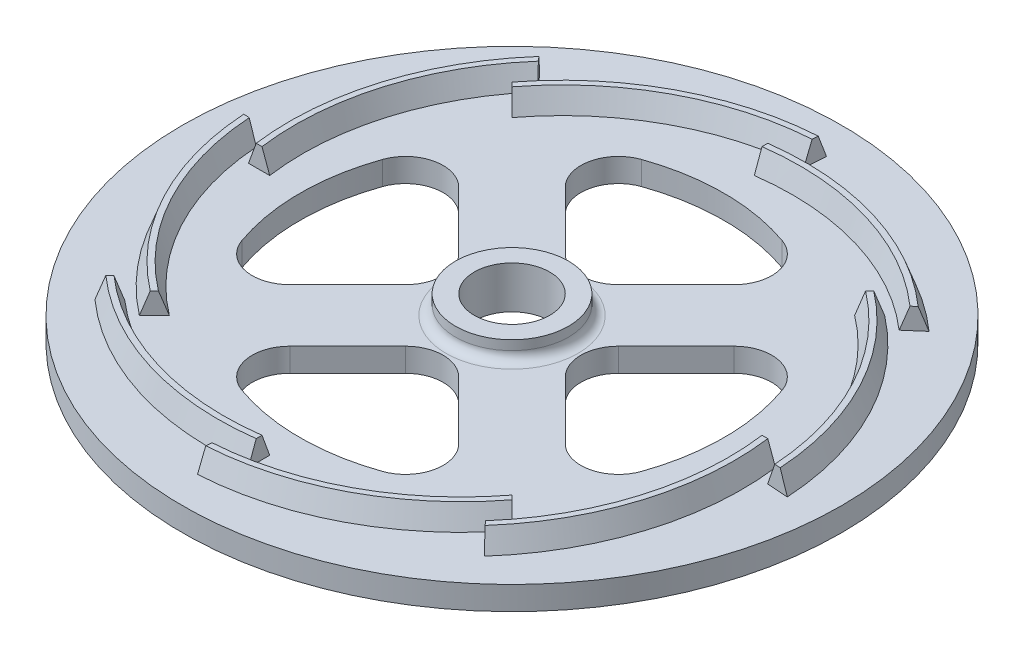
SolidWorks part; units mm, degrees
ref_plane "Front Plane" through (0, 0, 0) normal (0, 0, 1) x (1, 0, 0)
ref_plane "Top Plane" through (0, 0, 0) normal (0, 1, 0) x (1, 0, 0)
ref_plane "Right Plane" through (0, 0, 0) normal (1, 0, 0) x (0, 0, -1)
sketch "Sketch1" plane through (0, 0, 0) normal (0, 0, 1) x (1, 0, 0)
  line L0 (34.1131, 8.75) -> (33.2942, 11) construction
  line L1 (33.2942, 11) -> (32.6793, 11) construction
  line L2 (32.6793, 11) -> (31.8604, 8.75) construction
  line L3 (2.9867, 6.25) -> (52.0479, 6.25) construction
  line L4 (2.9867, 23.0023) -> (2.9867, -18.96) construction
  line L5 (34.1131, 8.75) -> (33.2942, 11)
  line L6 (33.2942, 11) -> (32.6793, 11)
  line L7 (32.6793, 11) -> (31.8604, 8.75)
  line L8 (2.9867, 6.25) -> (52.0479, 6.25) construction
  line L9 (2.9867, 23.0023) -> (2.9867, -18.96) construction
  line L10 (31.8604, 8.75) -> (34.1131, 8.75)
  line L11 (31.8604, 8.75) -> (31.8604, 6.25) construction
  line L12 (31.8604, 6.25) -> (34.1131, 6.25) construction
  line L13 (34.1131, 6.25) -> (34.1131, 8.75) construction
  line L14 (30.9715, 8.75) -> (30.1526, 11) construction
  line L15 (30.1526, 11) -> (29.5377, 11) construction
  line L16 (29.5377, 11) -> (28.7188, 8.75) construction
  line L17 (30.9715, 8.75) -> (30.1526, 11) construction
  line L18 (30.1526, 11) -> (29.5377, 11) construction
  line L19 (29.5377, 11) -> (28.7188, 8.75) construction
  line L20 (28.7188, 8.75) -> (30.9715, 8.75) construction
  line L21 (29.8451, 11) -> (29.8451, 8.75) construction
  line L22 (32.9867, 11) -> (32.9867, 8.75) construction
sketch "Sketch2" plane through (0, 0, 0) normal (0, 0, 1) x (1, 0, 0)
  line L0 (2.9867, 6.25) -> (37.9867, 6.25)
  line L1 (2.9867, 6.25) -> (52.0479, 6.25) construction
  line L2 (37.9867, 6.25) -> (37.9867, 8.75)
  line L4 (37.9867, 8.75) -> (2.9867, 8.75)
  line L5 (2.9867, 23.0023) -> (2.9867, -18.96) construction
  line L6 (2.9867, 8.75) -> (2.9867, 6.25) construction
  line L7 (2.9867, 6.25) -> (2.9867, 8.75)
  dimension "D1" = 2.5
  dimension "D2" = 70
revolve "Revolve1" add sketch "Sketch2" angle 360 about L6
sketch "Sketch3" plane through (0, 8.75, 0) normal (0, 1, 0) x (1, 0, 0)
  line L0 (2.9867, 0) -> (52.0479, 0) construction
  line L1 (2.9867, 39.0572) -> (2.9867, -41.5335) construction
  line L2 (-40.5207, 0) -> (49.0745, 0) construction
  line L11 (2.9867, 0) -> (24.1999, 21.2132) construction
  line L12 (2.9867, 0) -> (24.1999, -21.2132) construction
  line L13 (2.9867, 0) -> (-18.2265, -21.2132) construction
  line L14 (2.9867, 0) -> (-18.2265, 21.2132) construction
  line L15 (11.9534, 14.6236) -> (5.8151, 8.4853)
  line L16 (0.1583, 8.4853) -> (-5.98, 14.6236)
  line L17 (11.9534, -14.6236) -> (5.8151, -8.4853)
  line L18 (0.1583, -8.4853) -> (-5.98, -14.6236)
  line L19 (-11.6368, 8.9667) -> (-5.4986, 2.8284)
  line L20 (-5.4986, -2.8284) -> (-11.6368, -8.9667)
  line L21 (17.6103, 8.9667) -> (11.472, 2.8284)
  line L22 (11.472, -2.8284) -> (17.6103, -8.9667)
  circle A0 centre (2.9867, 0) radius 30 construction
  arc A1 (-18.2387, 7.4655) -> (-18.2387, -7.4655) centre (2.9867, 0) ccw
  arc A2 (10.4522, 21.2254) -> (-4.4787, 21.2254) centre (2.9867, 0) ccw
  arc A3 (24.2121, -7.4655) -> (24.2121, 7.4655) centre (2.9867, 0) ccw
  arc A4 (-4.4787, -21.2254) -> (10.4522, -21.2254) centre (2.9867, 0) ccw
  circle A5 centre (2.9867, 0) radius 4
  arc A6 (5.8151, 8.4853) -> (0.1583, 8.4853) centre (2.9867, 11.3137) cw
  arc A7 (11.9534, 14.6236) -> (10.4522, 21.2254) centre (9.125, 17.452) ccw
  arc A8 (-5.98, 14.6236) -> (-4.4787, 21.2254) centre (-3.1515, 17.452) cw
  arc A9 (-11.6368, 8.9667) -> (-18.2387, 7.4655) centre (-14.4653, 6.1383) ccw
  arc A10 (-11.6368, -8.9667) -> (-18.2387, -7.4655) centre (-14.4653, -6.1383) cw
  arc A11 (-5.98, -14.6236) -> (-4.4787, -21.2254) centre (-3.1515, -17.452) ccw
  arc A12 (11.9534, -14.6236) -> (10.4522, -21.2254) centre (9.125, -17.452) cw
  arc A13 (17.6103, -8.9667) -> (24.2121, -7.4655) centre (20.4387, -6.1383) ccw
  arc A14 (24.2121, 7.4655) -> (17.6103, 8.9667) centre (20.4387, 6.1383) ccw
  arc A15 (11.472, 2.8284) -> (11.472, -2.8284) centre (14.3004, 0) ccw
  arc A16 (5.8151, -8.4853) -> (0.1583, -8.4853) centre (2.9867, -11.3137) ccw
  arc A17 (-5.4986, 2.8284) -> (-5.4986, -2.8284) centre (-8.327, 0) cw
  point P28 (2.9867, 5.6569)
  point P31 (15.8148, 18.4849)
  point P44 (21.4716, -12.828)
  point P49 (8.6436, 0)
  point P52 (2.9867, -5.6569)
  point P55 (-2.6701, 0)
  dimension "D1" = 60
  dimension "D4" = 45
  dimension "D5" = 8
  dimension "D6" = 4
  dimension "D7" = 4
  dimension "D2" = 45
  dimension "D3" = 8
extrude "Cut-Extrude1" cut sketch "Sketch3" against normal through all
ref_plane "Plane2" through (1.4934, 0, 1.4934) normal (0.7071, 0, 0.7071) x (0, -1, 0)
sketch "Sketch8" plane through (1.4934, 0, 1.4934) normal (0.7071, 0, 0.7071) x (0, -1, 0)
  line L0 (-8.75, 33.2383) -> (-11, 32.4194)
  line L1 (-11, 32.4194) -> (-11, 31.8045)
  line L2 (-11, 31.8045) -> (-8.75, 30.9856)
  line L3 (-6.25, 2.1119) -> (-6.25, 51.1731) construction
  line L4 (-23.0023, 2.1119) -> (18.96, 2.1119) construction
  line L5 (-8.75, 30.9856) -> (-8.75, 33.2383)
  line L6 (-8.75, 30.9856) -> (-6.25, 30.9856) construction
  line L7 (-6.25, 30.9856) -> (-6.25, 33.2383) construction
  line L8 (-6.25, 33.2383) -> (-8.75, 33.2383) construction
  line L9 (-8.75, 30.0967) -> (-11, 29.2778) construction
  line L10 (-11, 29.2778) -> (-11, 28.6629) construction
  line L11 (-11, 28.6629) -> (-8.75, 27.844) construction
  line L12 (-8.75, 27.844) -> (-8.75, 30.0967) construction
  line L13 (-11, 28.9703) -> (-8.75, 28.9703) construction
  line L14 (-11, 32.1119) -> (-8.75, 32.1119) construction
  dimension "D1" = 26.8584
  dimension "D2" = 30
  dimension "D3" = 2.5
  dimension "D4" = 2.5
  dimension "D5" = 2.25
  dimension "D6" = 2.2527
  dimension "D7" = 0.6149
  dimension "D8" = 0.6149
  dimension "D9" = 2.2527
  dimension "D10" = 20
  dimension "D11" = 20
sketch "Sketch9" plane through (0, 8.75, 0) normal (0, 1, 0) x (1, 0, 0)
  line L0 (32.9867, 0) -> (32.0728, 6.8499) construction
  line L1 (31.8604, 0) -> (34.1131, 0) construction
  line L3 (32.9867, 0) -> (32.9867, -4.1628) construction
  line L4 (21.9785, 18.9918) -> (20.0119, 20.4955) construction
  line L5 (21.9785, 18.9918) -> (15.9547, 25.0156) construction
  line L6 (21.9785, 18.9918) -> (32.9867, 30) construction
  line L7 (-14.8261, -17.8129) -> (17.8129, 14.8261) construction
  line L8 (33.1826, -2) -> (32.9867, -2) construction
  arc A0 (32.9867, 0) -> (21.9785, 18.9918) centre (4.5552, -3.7936) ccw
  arc A1 (32.9867, 0) -> (33.1826, -2) centre (4.5552, -3.7936) cw
  dimension "D1" = 7.6
  dimension "D2" = 2
  dimension "D3" = 90
  dimension "D4" = 7.596
sweep "Sweep2" add profiles "Sketch1" path "Sketch9"
pattern_circular "CirPattern1" count 8 over 360 about axis through (2.9867, 6.25, 0) along (0, 1, 0) of "Sweep2"
sketch "Sketch11" plane through (0, 8.75, 0) normal (0, 1, 0) x (1, 0, 0)
  circle A0 centre (2.9867, 0) radius 4
  circle A1 centre (2.9867, 0) radius 6
  dimension "D1" = 12
  dimension "D2" = 8
extrude "Boss-Extrude1" add sketch "Sketch11" along normal blind 2
fillet "Fillet1" radius 1 1 edges at (8.9867, 8.75, 0)
